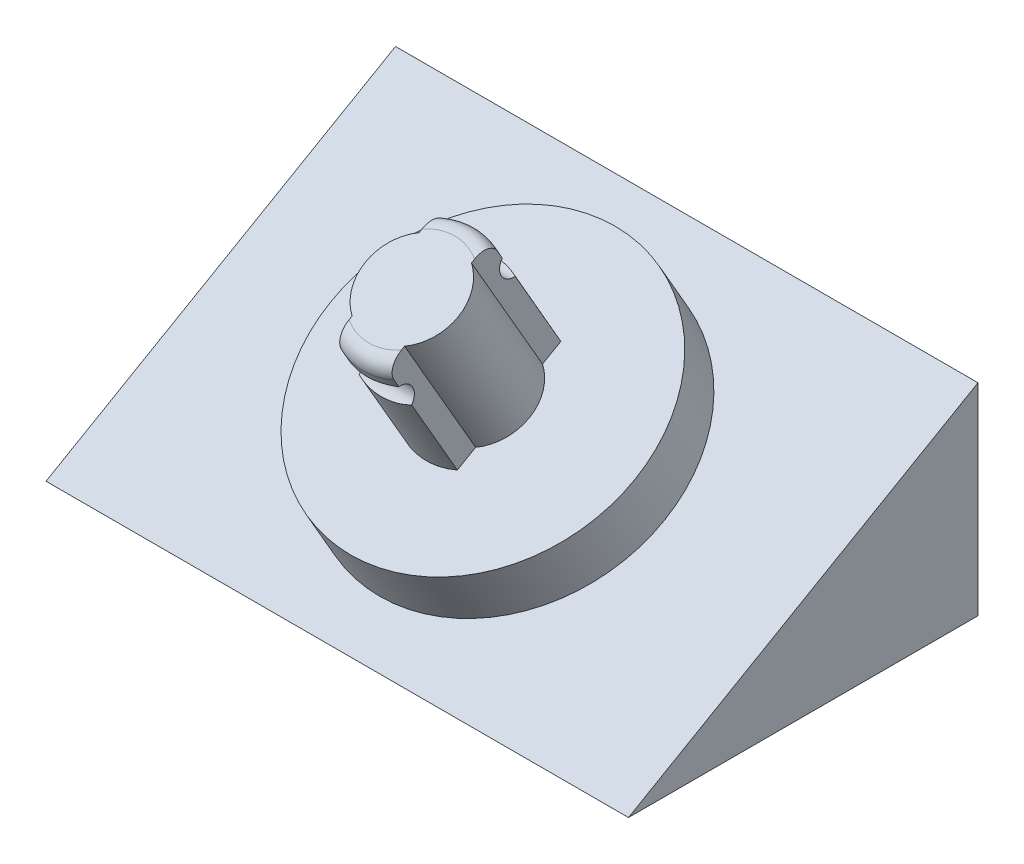
SolidWorks part; units mm, degrees
ref_plane "Front Plane" through (0, 0, 0) normal (0, 0, 1) x (1, 0, 0)
ref_plane "Top Plane" through (0, 0, 0) normal (0, 1, 0) x (1, 0, 0)
ref_plane "Right Plane" through (0, 0, 0) normal (1, 0, 0) x (0, 0, -1)
sketch "Sketch8" plane through (0, 0, 0) normal (1, 0, 0) x (0, 0, -1)
  line L0 (-9, 0) -> (9, 10.3923)
  line L1 (9, 10.3923) -> (9, 0)
  line L2 (9, 0) -> (-9, 0)
  dimension "D1" = 18
  dimension "D2" = 30
extrude "Boss-Extrude4" add sketch "Sketch8" along normal mid plane 30
sketch "Sketch3" plane through (0, 1.6402, 6.159) normal (0, -0.866, -0.5) x (1, 0, 0)
  line L0 (0, 3.2805) -> (0, -17.5041) construction
  line L1 (15, 3.2805) -> (-15, 3.2805) construction
  line L2 (15, -17.5041) -> (-15, -17.5041) construction
  circle A0 centre (0, -7.1118) radius 7.86
  dimension "D1" = 15.72
extrude "Boss-Extrude2" add sketch "Sketch3" against normal blind 3
sketch "Sketch5" plane through (0, 6.4952, 3.75) normal (0, 0.866, 0.5) x (1, 0, 0)
  line L0 (1.35, 4.5884) -> (1.35, 5.6749)
  line L2 (-1.35, -0.4788) -> (-1.35, 0.6077)
  line L4 (1.35, -0.4788) -> (1.35, 0.6077)
  line L7 (-1.35, 4.5884) -> (-1.35, 5.6749)
  arc A0 (-1.35, 4.5884) -> (-1.35, 0.6077) centre (0, 2.5981) ccw
  arc A1 (1.35, 0.6077) -> (1.35, 4.5884) centre (0, 2.5981) ccw
  arc A2 (-1.35, -0.4788) -> (1.35, -0.4788) centre (0, 2.5981) ccw
  arc A3 (1.35, 5.6749) -> (-1.35, 5.6749) centre (0, 2.5981) ccw
  circle A6 centre (0, 2.5981) radius 7.86 construction
  dimension "D1" = 4.81
  dimension "D3" = 6.72
  dimension "D2" = 2.7
extrude "Boss-Extrude3" add sketch "Sketch5" along normal blind 7.32
sketch "Sketch6" plane through (1.35, 0, 0) normal (1, 0, 0) x (0, 0, -1)
  line L3 (-1.2752, 14.1248) -> (-7.0948, 10.7648) construction
  line L4 (-3.4363, 15.1287) -> (-2.4954, 15.672) construction
  line L7 (1.4098, 9.4742) -> (-2.2502, 15.8135) construction
  line L16 (-8.0698, 12.4535) -> (-4.4098, 6.1142) construction
  line L17 (-7.8246, 12.5951) -> (-8.0698, 12.4535) construction
  line L19 (-7.8246, 12.5951) -> (-8.0698, 12.4535) construction
  line L20 (5.307, 11.7242) -> (-8.307, 3.8642) construction
  line L23 (-7.8246, 12.5951) -> (-4.1646, 6.2558) construction
  line L24 (5.307, 11.7242) -> (-8.307, 3.8642) construction
  circle A0 centre (-1.2752, 14.1248) radius 0.715
  circle A1 centre (-7.0948, 10.7648) radius 0.715
  point P8 (-1.8944, 13.7673)
  point P9 (-6.4756, 11.1223)
  dimension "D1" = 5.29
  dimension "D2" = 5.37
extrude "Cut-Extrude2" cut sketch "Sketch6" against normal through all
fillet "Fillet5" radius 0.8 2 edges at (0, 15.8135, 2.2502) (0, 12.4535, 8.0698)
